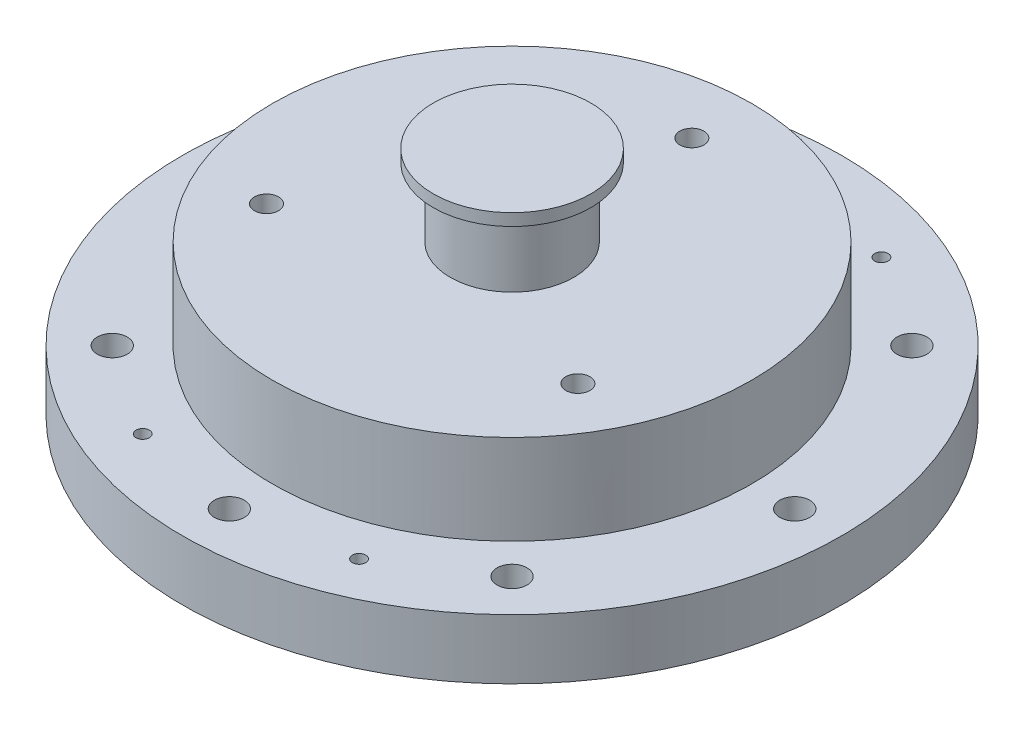
SolidWorks part; units mm, degrees
ref_plane "Front Plane" through (0, 0, 0) normal (0, 0, 1) x (1, 0, 0)
ref_plane "Top Plane" through (0, 0, 0) normal (0, 1, 0) x (1, 0, 0)
ref_plane "Right Plane" through (0, 0, 0) normal (1, 0, 0) x (0, 0, -1)
sketch "Sketch1" plane through (0, 0, 0) normal (0, 1, 0) x (1, 0, 0)
  circle A1 centre (0, 0) radius 50.8
  dimension "D1" = 101.6
extrude "Boss-Extrude1" add sketch "Sketch1" along normal blind 25.4
sketch "Sketch2" plane through (0, 0, 0) normal (0, -1, 0) x (1, 0, 0)
  circle A0 centre (0, 0) radius 50.8
  circle A1 centre (0, 0) radius 69.85
  dimension "D1" = 139.7
extrude "Boss-Extrude2" add sketch "Sketch2" against normal blind 12.7
sketch "Sketch4" plane through (0, 0, 0) normal (0, -1, 0) x (1, 0, 0)
  circle A0 centre (0, -59.9186) radius 3.175
  circle A1 centre (-42.3688, -42.3688) radius 3.175
  circle A2 centre (-59.9186, 0) radius 3.175
  circle A3 centre (-42.3688, 42.3688) radius 3.175
  circle A4 centre (0, 59.9186) radius 3.175
  circle A5 centre (42.3688, 42.3688) radius 3.175
  circle A6 centre (59.9186, 0) radius 3.175
  circle A7 centre (42.3688, -42.3688) radius 3.175
  point P35 (0, 0)
  dimension "D2" = 6.35
  dimension "D1" = 59.9186
  dimension "D3" = 8
extrude "Cut-Extrude2" cut sketch "Sketch4" against normal up to next
sketch "Sketch5" plane through (0, 25.4, 0) normal (0, 1, 0) x (1, 0, 0)
  circle A0 centre (0, 0) radius 12.827
  dimension "D1" = 25.654
extrude "Cut-Extrude3" cut sketch "Sketch5" against normal blind 19.05 from offset 0
sketch "Sketch6" plane through (0, 6.35, 0) normal (0, 1, 0) x (1, 0, 0)
  circle A0 centre (0, 0) radius 1.5875
  dimension "D1" = 3.175
extrude "Cut-Extrude4" cut sketch "Sketch6" against normal up to next
sketch "Sketch34" plane through (0, 25.4, 0) normal (0, 1, 0) x (1, 0, 0)
  circle A0 centre (0, 0) radius 13.081
  circle A1 centre (0, 0) radius 4.7625
  dimension "D1" = 26.162
  dimension "D2" = 9.525
extrude "Boss-Extrude3" add sketch "Sketch34" along normal blind 19.05
cosmetic thread "Cosmetic Thread4" parameters "D2"=23.1953
sketch "Sketch40" plane through (0, 25.4, 0) normal (0, 1, 0) x (1, 0, 0)
  circle A0 centre (0, 0) radius 50.8
extrude "Boss-Extrude5" add sketch "Sketch40" along normal blind 6.35
sketch "Sketch38" plane through (0, 44.45, 0) normal (0, 1, 0) x (1, 0, 0)
  circle A0 centre (0, 0) radius 6.2484
  dimension "D1" = 12.4968
extrude "Boss-Extrude4" add sketch "Sketch38" along normal blind 1.905 separate body
sketch "Sketch39" plane through (0, 46.355, 0) normal (0, 1, 0) x (1, 0, 0)
  circle A0 centre (0, 0) radius 4.7625
  dimension "D1" = 9.525
extrude "Cut-Extrude7" cut sketch "Sketch39" against normal blind 6.35
sketch "Sketch41" plane through (0, 31.75, 0) normal (0, 1, 0) x (1, 0, 0)
  circle A0 centre (0, 0) radius 4.7625
  dimension "D1" = 9.525
extrude "Cut-Extrude8" cut sketch "Sketch41" against normal blind 6.35
sketch "Sketch42" plane through (0, 0, 0) normal (0, -1, 0) x (1, 0, 0)
  circle A0 centre (0, 0) radius 23.7871
  dimension "D1" = 47.5742
extrude "Cut-Extrude9" cut sketch "Sketch42" against normal blind 6.477
hole_wizard "#10-24 Tapped Hole1" positions "Sketch44" profile "Sketch45" tap size "#10-24" standard "ANSI Inch"
sketch "Sketch44" plane through (0, 6.477, 0) normal (0, -1, 0) x (-1, 0, 0)
  line L0 (0, 0) -> (0, -35.56) construction
  line L2 (0, 0) -> (0, 30.48) construction
  line L4 (0, 0) -> (-27.94, 0) construction
  line L6 (0, 0) -> (30.48, 0) construction
  circle A0 centre (0, 0) radius 17.4625 construction
  point P0 (0, -17.4625)
  point P2 (-17.4625, 0)
  point P4 (0, 17.4625)
  point P6 (17.4625, 0)
  dimension "D1" = 34.925
sketch "Sketch45" plane through (0, 6.477, 17.4625) normal (1, 0, 0) x (0, 0, -1)
  line L0 (0, 0) -> (0, 13.8408)
  line L1 (0, 13.8408) -> (1.8986, 12.7)
  line L2 (1.8986, 12.7) -> (1.8986, 0)
  line L5 (1.8986, 0) -> (0, 0)
  line L10 (0, 13.8408) -> (-1.8987, 12.7) construction
  line L11 (0, -6.35) -> (0, 107.95) construction
  dimension "Tap Drill Dia." = 3.7973
  dimension "Tap Drill Depth" = 12.7
  dimension "Drill Angle" = 118
cosmetic thread "Hole Thread1" parameters "D1"=9.652, "D2"=4.826
cosmetic thread "Hole Thread2" parameters "D1"=9.652, "D2"=4.826
cosmetic thread "Hole Thread3" parameters "D1"=9.652, "D2"=4.826
cosmetic thread "Hole Thread4" parameters "D1"=9.652, "D2"=4.826
sketch "Sketch46" plane through (0, 0, 0) normal (0, -1, 0) x (1, 0, 0)
  line L0 (0, -83.82) -> (0, 83.82) construction
  line L1 (34.3522, -82.9336) -> (-34.3522, 82.9336) construction
  line L2 (-32.8909, -79.4057) -> (32.8909, 79.4057) construction
  circle A0 centre (0, 0) radius 59.9186 construction
  circle A1 centre (-22.9299, 55.3576) radius 3.175
  circle A2 centre (22.9299, 55.3576) radius 3.175
  circle A3 centre (-22.9299, -55.3576) radius 3.175
  circle A4 centre (22.9299, -55.3576) radius 3.175
  point P7 (0, 0)
  point P10 (0, 0)
  point P12 (0, 0)
  dimension "D1" = 119.8372
  dimension "D4" = 6.35
  dimension "D5" = 6.35
  dimension "D6" = 6.35
  dimension "D7" = 6.35
  dimension "D2" = 22.5
  dimension "D3" = 22.5
extrude "Cut-Extrude10" cut sketch "Sketch46" against normal blind 6.35
hole_wizard "1/4-20 Tapped Hole1" positions "Sketch47" profile "Sketch48" tap size "1/4-20" standard "ANSI Inch"
sketch "Sketch47" plane through (0, 31.75, 0) normal (0, 1, 0) x (1, 0, 0)
  line L0 (0, 0) -> (0, 45.3569) construction
  line L2 (0, 0) -> (-40.0078, -23.0985) construction
  line L4 (0, 0) -> (38.662, -22.3215) construction
  circle A0 centre (0, 0) radius 38.1 construction
  point P0 (0, 38.1)
  point P2 (32.9956, -19.05)
  point P4 (-32.9956, -19.05)
  dimension "D1" = 76.2
  dimension "D2" = 120
  dimension "D3" = 120
sketch "Sketch48" plane through (0, 31.75, -38.1) normal (1, 0, 0) x (0, 0, 1)
  line L0 (0, 0) -> (0, 15.5038)
  line L1 (0, 15.5038) -> (2.5527, 13.97)
  line L2 (2.5527, 13.97) -> (2.5527, 0)
  line L5 (2.5527, 0) -> (0, 0)
  line L10 (0, 15.5038) -> (-2.5527, 13.97) construction
  line L11 (0, -6.35) -> (0, 107.95) construction
  dimension "Tap Drill Dia." = 5.1054
  dimension "Tap Drill Depth" = 13.97
  dimension "Drill Angle" = 118
cosmetic thread "Hole Thread5" parameters "D1"=12.7, "D2"=6.35
cosmetic thread "Hole Thread6" parameters "D1"=12.7, "D2"=6.35
cosmetic thread "Hole Thread7" parameters "D1"=12.7, "D2"=6.35
sketch "Sketch49" plane through (0, 6.477, 0) normal (0, -1, 0) x (1, 0, 0)
  circle A0 centre (0, 0) radius 23.8252
  dimension "D1" = 47.6504
extrude "Cut-Extrude11" cut sketch "Sketch49" against normal blind 3.937 from surface at 6.477 starting at face at (22.9299, 0, 52.1826)
sketch "Sketch50" plane through (0, 6.35, 0) normal (0, -1, 0) x (1, 0, 0)
  circle A0 centre (-22.9299, 55.3576) radius 1.4097
  circle A1 centre (22.9299, 55.3576) radius 1.4097
  circle A2 centre (-22.9299, -55.3576) radius 1.4097
  circle A3 centre (22.9299, -55.3576) radius 1.4097
  dimension "D1" = 2.8194
  dimension "D2" = 2.8194
  dimension "D3" = 2.8194
  dimension "D4" = 2.8194
extrude "Cut-Extrude12" cut sketch "Sketch50" against normal through all
sketch "Sketch51" plane through (0, 46.355, 0) normal (0, 1, 0) x (1, 0, 0)
  circle A0 centre (0, 0) radius 16.694
extrude "Boss-Extrude6" add sketch "Sketch51" along normal blind 2.54
